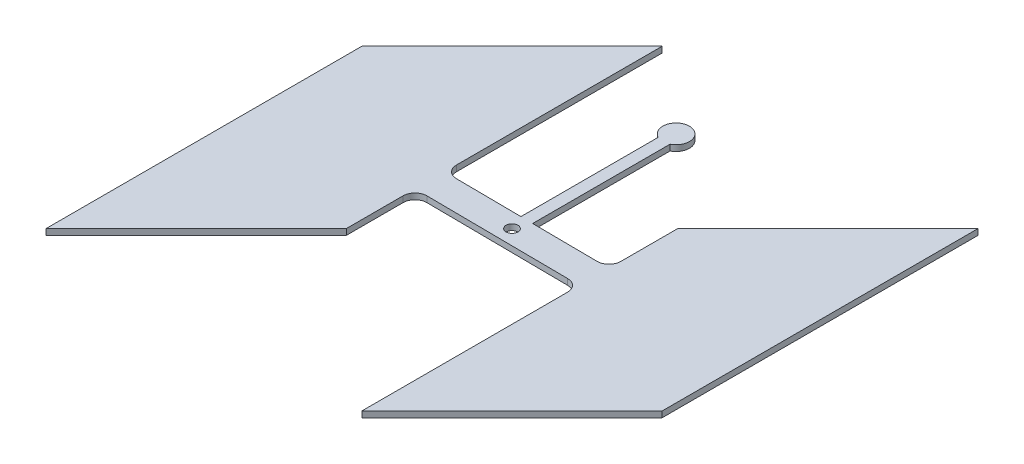
SolidWorks part; units mm, degrees
material "Cedar"
ref_plane "Front Plane" through (0, 0, 0) normal (0, 0, 1) x (1, 0, 0)
ref_plane "Top Plane" through (0, 0, 0) normal (0, 1, 0) x (1, 0, 0)
ref_plane "Right Plane" through (0, 0, 0) normal (1, 0, 0) x (0, 0, -1)
sketch "Sketch1" plane through (0, 0, 0) normal (0, 1, 0) x (1, 0, 0)
  line L0 (0, 31.75) -> (0, -31.75) construction
  line L1 (-152.1676, -30.3998) -> (152.6184, -33.1042)
  line L2 (-152.6184, 33.1042) -> (152.1676, 30.3998)
  line L8 (0, 0) -> (177.793, 0) construction
  line L9 (0, 0) -> (-177.793, 0) construction
  line L16 (177.793, 500) -> (177.793, -500)
  line L17 (-177.793, 500) -> (-177.793, -500)
  line L18 (-500, -500) -> (500, -500)
  line L19 (-177.793, 500) -> (-500, 500)
  line L20 (-500, 500) -> (-500, -500)
  line L21 (177.793, 500) -> (500, 500)
  line L22 (500, 500) -> (500, -500)
  line L23 (-177.793, 500) -> (-500, 177.793)
  line L24 (-500, -500) -> (-177.793, -177.793)
  line L25 (177.793, -500) -> (500, -177.793)
  line L26 (500, 500) -> (177.793, 177.793)
  line L27 (-177.793, -55.7988) -> (-177.793, -177.793)
  line L28 (-177.793, 58.5032) -> (-177.793, 500)
  line L29 (177.793, 55.7988) -> (177.793, 177.793)
  line L30 (177.793, -58.5032) -> (177.793, -500)
  line L57 (0, 31.75) -> (0, 352.138) construction
  line L58 (12.7116, 326.5077) -> (12.7116, 31.6372)
  line L59 (-12.7116, 326.5077) -> (-12.7116, 31.6372)
  line L60 (12.7116, 40.4802) -> (-12.7116, 40.4802) construction
  arc A0 (152.1676, 30.3998) -> (177.793, 55.7988) centre (152.393, 55.7988) ccw
  arc A1 (-152.6184, 33.1042) -> (-177.793, 58.5032) centre (-152.393, 58.5032) cw
  arc A2 (-152.1676, -30.3998) -> (-177.793, -55.7988) centre (-152.393, -55.7988) ccw
  arc A3 (152.6184, -33.1042) -> (177.793, -58.5032) centre (152.393, -58.5032) cw
  circle A4 centre (0, 0) radius 12.7
  circle A5 centre (0, 352.138) radius 28.6094
  dimension "D1" = 25.4
extrude "Boss-Extrude1" add sketch "Sketch1" along normal blind 12.7 contours L20 L24 L17 L23 | L1 A3 L16 A0 L2 A1 L17 A2 | L22 L26 L16 L25 | A5 L59 L2 L58 | A5
